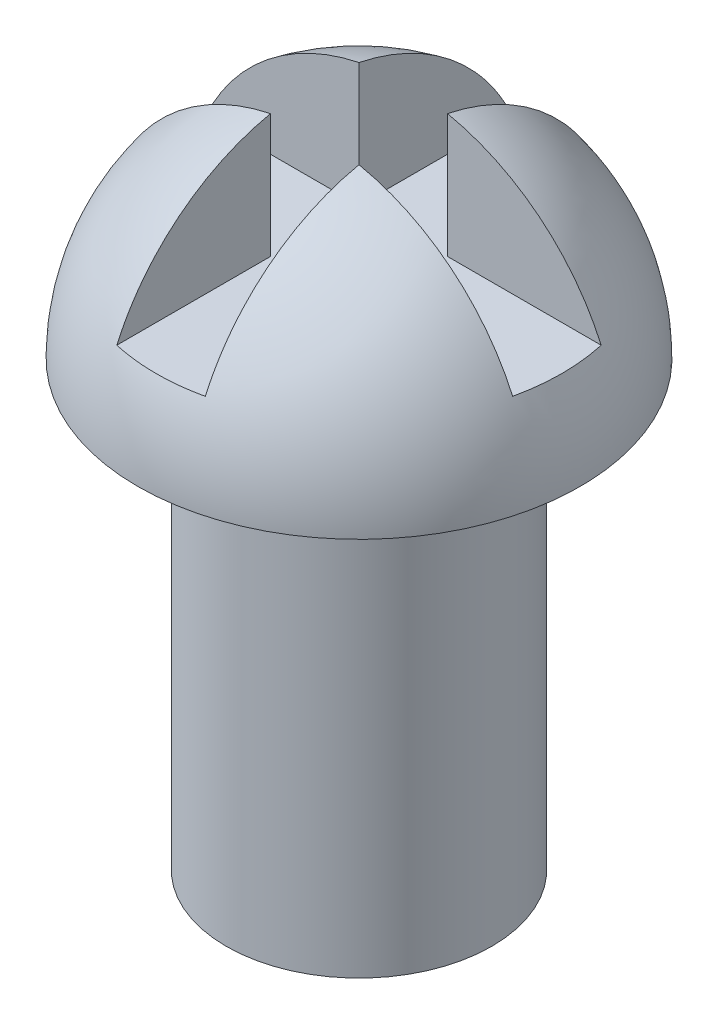
SolidWorks part; units mm, degrees
ref_plane "Front Plane" through (0, 0, 0) normal (0, 0, 1) x (1, 0, 0)
ref_plane "Top Plane" through (0, 0, 0) normal (0, 1, 0) x (1, 0, 0)
ref_plane "Right Plane" through (0, 0, 0) normal (1, 0, 0) x (0, 0, -1)
sketch "Sketch1" plane through (0, 0, 0) normal (0, 1, 0) x (1, 0, 0)
  circle A0 centre (0, 0) radius 1.5
  dimension "D1" = 3
extrude "Boss-Extrude1" add sketch "Sketch1" along normal blind 5
sketch "Sketch2" plane through (0, 5, 0) normal (0, 1, 0) x (1, 0, 0)
  line L0 (0, 2.5) -> (0, -2.5)
  arc A0 (0, -2.5) -> (0, 2.5) centre (0, 0) ccw
  dimension "D1" = 5
revolve "Revolve1" add sketch "Sketch2" angle 180 about L0
ref_plane "Plane1" through (0, 9, 0) normal (0, 1, 0) x (1, 0, 0)
sketch "Sketch3" plane through (0, 9, 0) normal (0, 1, 0) x (1, 0, 0)
  line L0 (0.5, 0.5) -> (5.63, 0.5)
  line L1 (-0.5, 4.674) -> (0.5, 4.674)
  line L2 (-0.5, 4.674) -> (-0.5, 0.5)
  line L3 (-0.5, -4.8333) -> (0.5, -4.8333)
  line L4 (0.5, 4.674) -> (0.5, 0.5)
  line L5 (-4.8333, 0.5) -> (-0.5, 0.5)
  line L6 (-4.8333, 0.5) -> (-4.8333, -0.5)
  line L7 (-4.8333, -0.5) -> (-0.5, -0.5)
  line L8 (5.63, 0.5) -> (5.63, -0.5)
  line L9 (-0.5, -0.5) -> (-0.5, -4.8333)
  line L10 (0.5, -0.5) -> (5.63, -0.5)
  line L11 (0.5, -0.5) -> (0.5, -4.8333)
  dimension "D1" = 1
  dimension "D2" = 0.5
  dimension "D3" = 1
  dimension "D4" = 0.5
extrude "Cut-Extrude1" cut sketch "Sketch3" against normal blind 3
